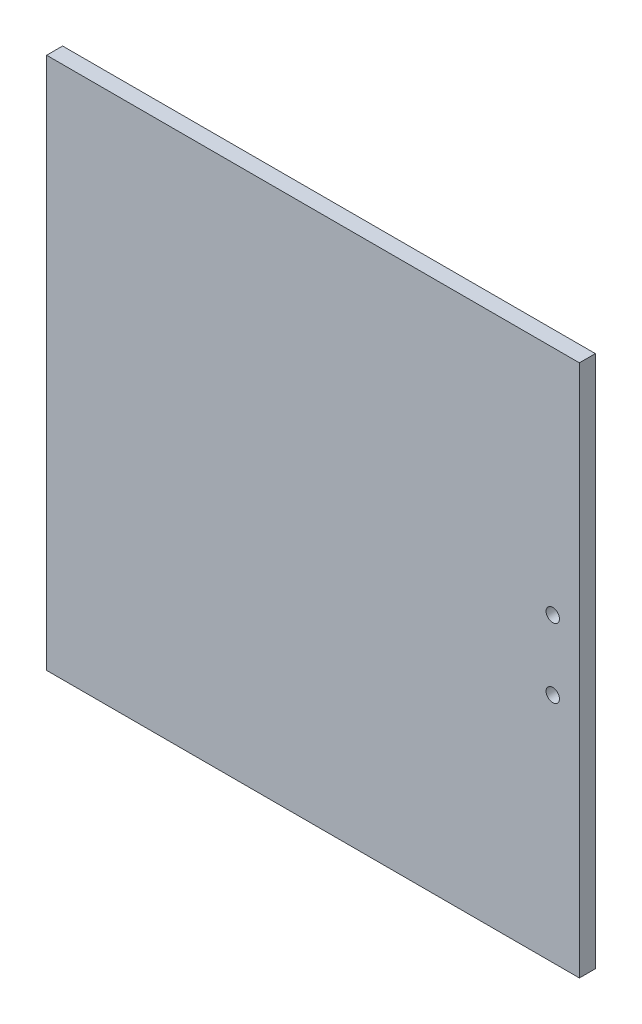
SolidWorks part; units mm, degrees
material "ABS"
ref_plane "Front Plane" through (0, 0, 0) normal (0, 0, 1) x (1, 0, 0)
ref_plane "Top Plane" through (0, 0, 0) normal (0, 1, 0) x (1, 0, 0)
ref_plane "Right Plane" through (0, 0, 0) normal (1, 0, 0) x (0, 0, -1)
sketch "Sketch1" plane through (0, 0, 0) normal (0, 0, 1) x (1, 0, 0)
  line L0 (90, 13) -> (90, -13) construction
  line L1 (-100, -100) -> (100, -100)
  line L2 (-100, -100) -> (-100, 100)
  line L3 (-100, 100) -> (100, 100)
  line L4 (100, -100) -> (100, 100)
  line L5 (-100, -100) -> (100, 100) construction
  line L6 (-100, 100) -> (100, -100) construction
  circle A0 centre (90, 13) radius 2.5
  circle A1 centre (90, -13) radius 2.5
  point P0 (0, 0)
  point P10 (90, 0)
  point P11 (100, 0)
  dimension "D2" = 5
  dimension "D1" = 200
  dimension "D3" = 26
  dimension "D4" = 10
extrude "Boss-Extrude1" add sketch "Sketch1" along normal blind 6
